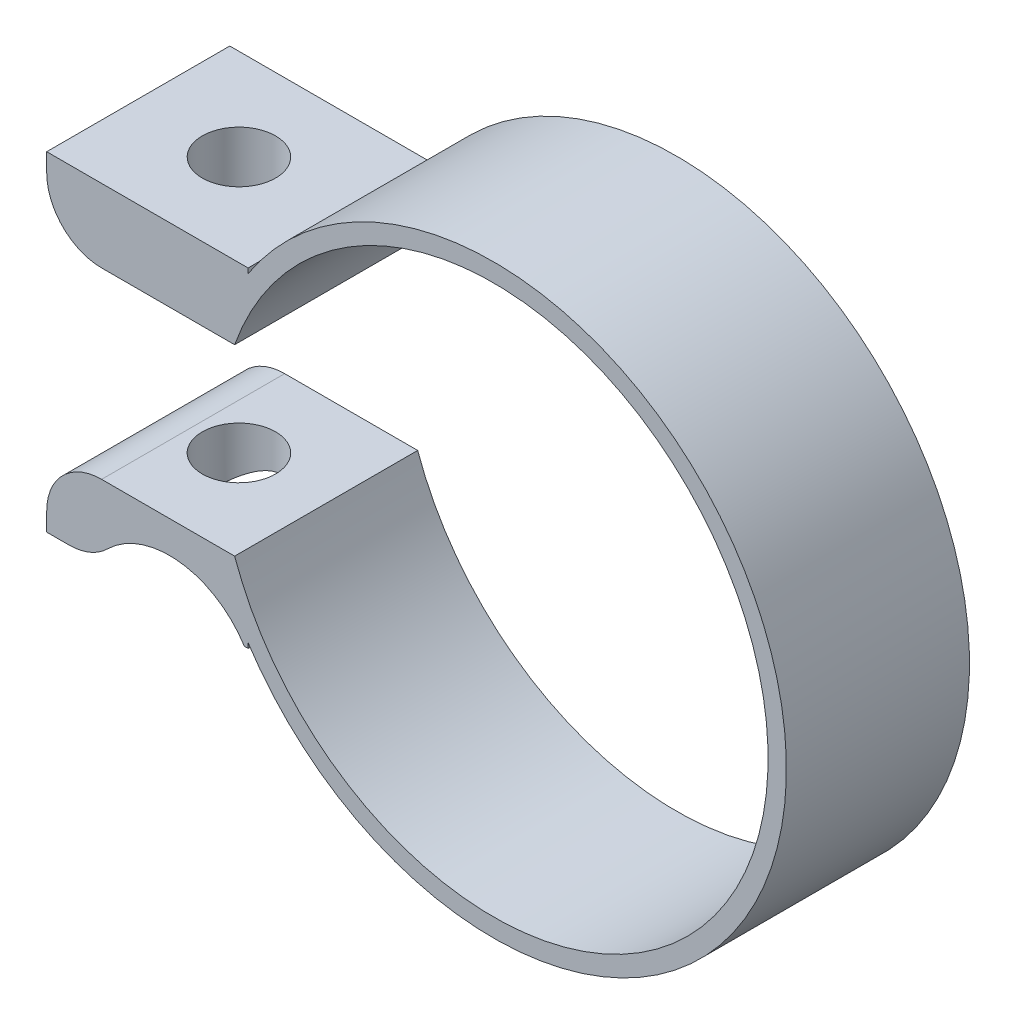
SolidWorks part; units mm, degrees
material "AISI 304"
ref_plane "Alzado" through (0, 0, 0) normal (0, 0, 1) x (1, 0, 0)
ref_plane "Planta" through (0, 0, 0) normal (0, 1, 0) x (1, 0, 0)
ref_plane "Vista lateral" through (0, 0, 0) normal (1, 0, 0) x (0, 0, -1)
sketch "Croquis1" plane through (0, 0, 0) normal (0, 0, 1) x (1, 0, 0)
  line L0 (16, 0) -> (15, 0)
  line L1 (-24.4075, 9) -> (-24.4075, 5)
  line L2 (-13.4075, -9) -> (-24.4075, -9)
  line L3 (-13.4075, -9) -> (-13.4075, -8.7314)
  line L4 (-13.4075, 9) -> (-24.4075, 9)
  line L5 (-24.4075, -9) -> (-24.4075, -5)
  line L6 (-24.4075, 5) -> (-24.4075, 9)
  line L7 (-24.4075, -5) -> (-14.1421, -5)
  line L8 (-13.4075, 9) -> (-13.4075, 8.7314)
  line L9 (-15.1987, 5) -> (-24.4075, 5)
  line L10 (-24.4075, -9) -> (-24.4075, -5)
  line L11 (-13.4075, -9) -> (-13.4075, -8.7314)
  line L12 (-15.1987, -5) -> (-24.4075, -5)
  line L13 (-13.4075, 8.7314) -> (-13.4075, 9)
  line L14 (-14.1421, 5) -> (-24.4075, 5)
  arc A0 (-15.1987, -5) -> (-15.1987, 5) centre (0, 0) ccw
  arc A1 (-14.1421, -5) -> (-14.1421, 5) centre (0, 0) ccw
  circle A2 centre (0, 0) radius 16 construction
  circle A3 centre (0, 0) radius 15 construction
  point P7 (-18.9075, 0)
  dimension "D1" = 32
  dimension "D3" = 18
  dimension "D4" = 11
  dimension "D2" = 1
extrude "Saliente-Extruir4" add sketch "Croquis1" along normal blind 10 contours A0 L8 L4 L1 L9 | A1 L0 A0 L14 | A0 L7 L5 L2 L3 | A1 L7 A0 L0
fillet "Redondeo4" radius 3 2 edges at (-24.4075, -5, 5) (-24.4075, 5, 5)
sketch "Croquis4" plane through (0, 9, 0) normal (0, 1, 0) x (1, 0, 0)
  circle A0 centre (-18.9075, -5) radius 2
  dimension "D1" = 4
extrude "Cortar-Extruir1" cut sketch "Croquis4" against normal blind 21
sketch "Croquis5" plane through (0, 0, 0) normal (0, 0, -1) x (-1, 0, 0)
  circle A1 centre (17.699, -11.5824) radius 4.8363
extrude "Cortar-Extruir2" cut sketch "Croquis5" against normal blind 21
fillet "Redondeo5" radius 3 1 edges at (-21.7881, -9, 5)
